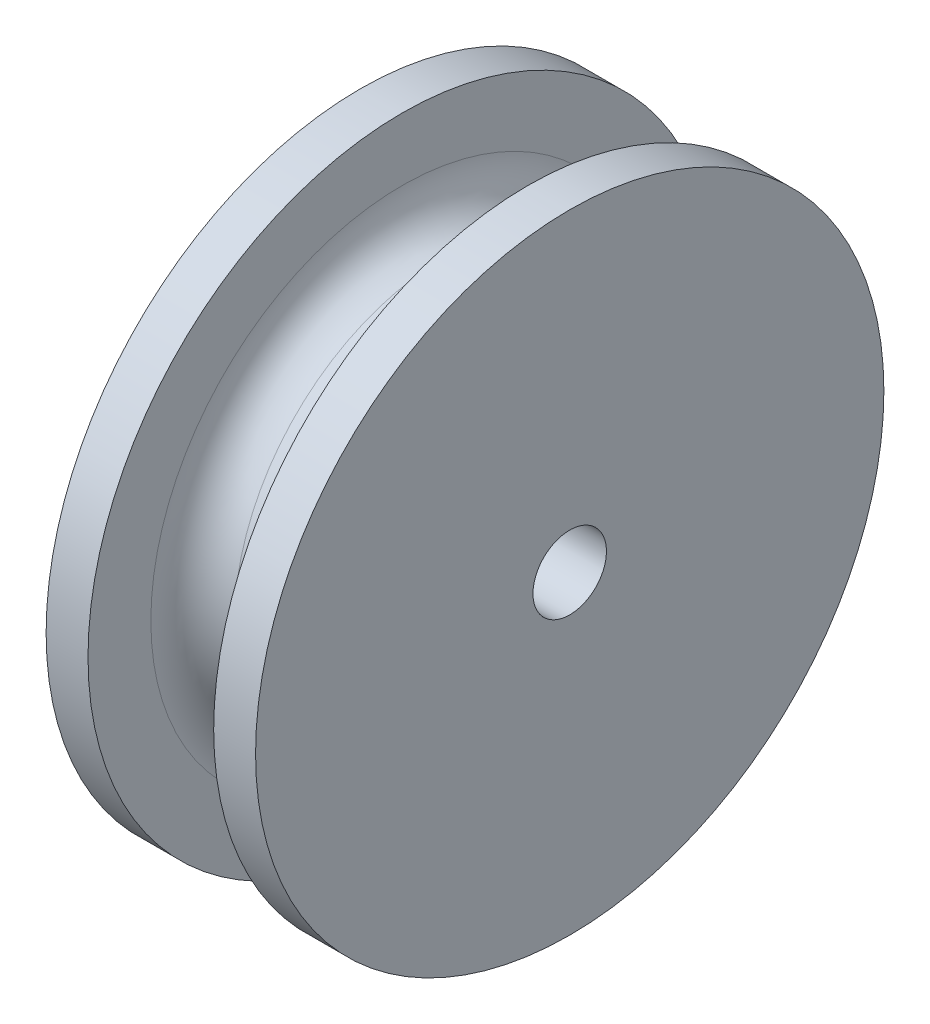
SolidWorks part; units mm, degrees
ref_plane "Front Plane" through (0, 0, 0) normal (0, 0, 1) x (1, 0, 0)
ref_plane "Top Plane" through (0, 0, 0) normal (0, 1, 0) x (1, 0, 0)
ref_plane "Right Plane" through (0, 0, 0) normal (1, 0, 0) x (0, 0, -1)
sketch "Sketch1" plane through (0, 0, 0) normal (0, 0, 1) x (1, 0, 0)
  line L0 (-9.2417, 0) -> (9.0521, 0) construction
  line L1 (-1, 10) -> (1, 10)
  line L2 (3, 12) -> (3, 15)
  line L3 (3, 15) -> (5, 15)
  line L4 (5, 15) -> (5, 1.7536)
  line L5 (5, 1.7536) -> (-5, 1.7536)
  line L6 (-5, 1.7536) -> (-5, 15)
  line L7 (-5, 15) -> (-3, 15)
  line L8 (-3, 15) -> (-3, 12)
  arc A0 (1, 10) -> (3, 12) centre (1, 12) ccw
  arc A1 (-1, 10) -> (-3, 12) centre (-1, 12) cw
  point P5 (0, 1.7536)
  point P12 (0, 10)
  point P13 (-4, 15)
  dimension "D6" = 2
  dimension "D1" = 10
  dimension "D2" = 10
  dimension "D3" = 15
  dimension "D4" = 15
  dimension "D5" = 2
revolve "Revolve1" add sketch "Sketch1" angle 360 about L0
